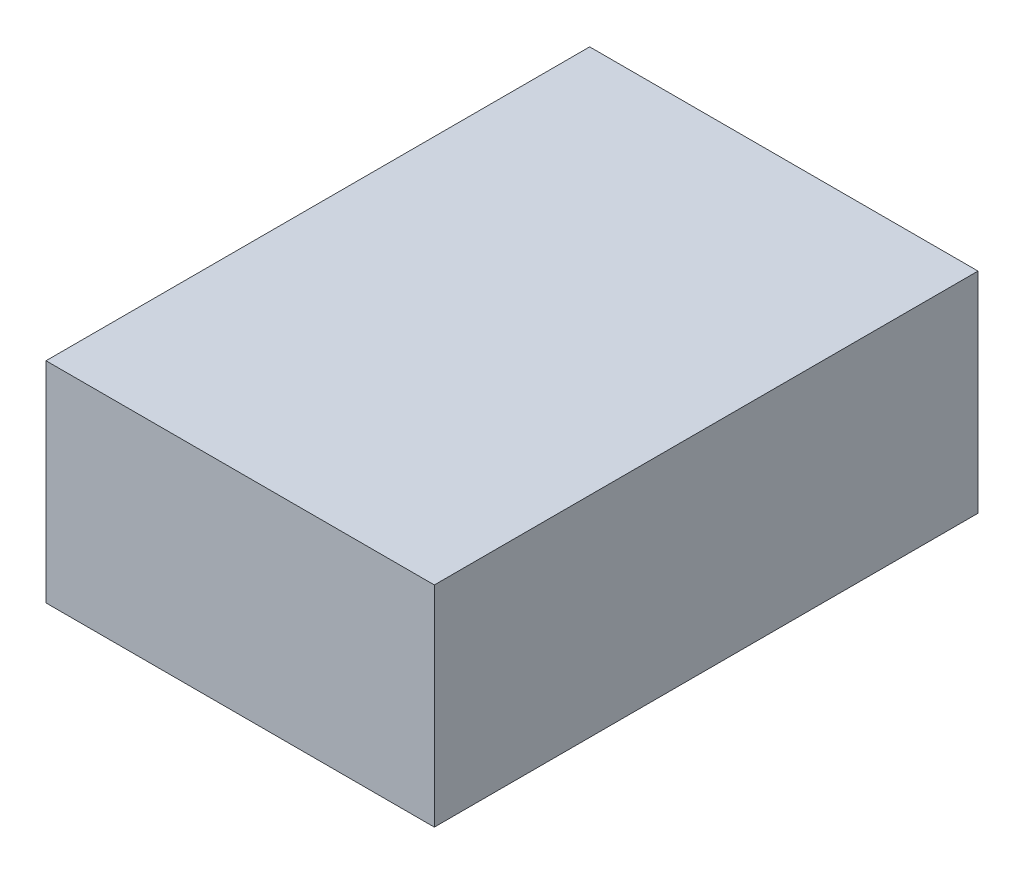
SolidWorks part; units mm, degrees
ref_plane "Front Plane" through (0, 0, 0) normal (0, 0, 1) x (1, 0, 0)
ref_plane "Top Plane" through (0, 0, 0) normal (0, 1, 0) x (1, 0, 0)
ref_plane "Right Plane" through (0, 0, 0) normal (1, 0, 0) x (0, 0, -1)
sketch "Sketch1" plane through (0, 0, 0) normal (0, 0, 1) x (1, 0, 0)
  line L1 (-6.35, 3.43) -> (6.35, 3.43)
  line L2 (-6.35, 3.43) -> (-6.35, -3.43)
  line L3 (-6.35, -3.43) -> (6.35, -3.43)
  line L4 (6.35, 3.43) -> (6.35, -3.43)
  line L5 (-6.35, 3.43) -> (6.35, -3.43) construction
  line L6 (-6.35, -3.43) -> (6.35, 3.43) construction
  point P0 (0, 0)
  dimension "D1" = 12.7
  dimension "D2" = 6.86
extrude "Boss-Extrude1" add sketch "Sketch1" along normal blind 17.78
